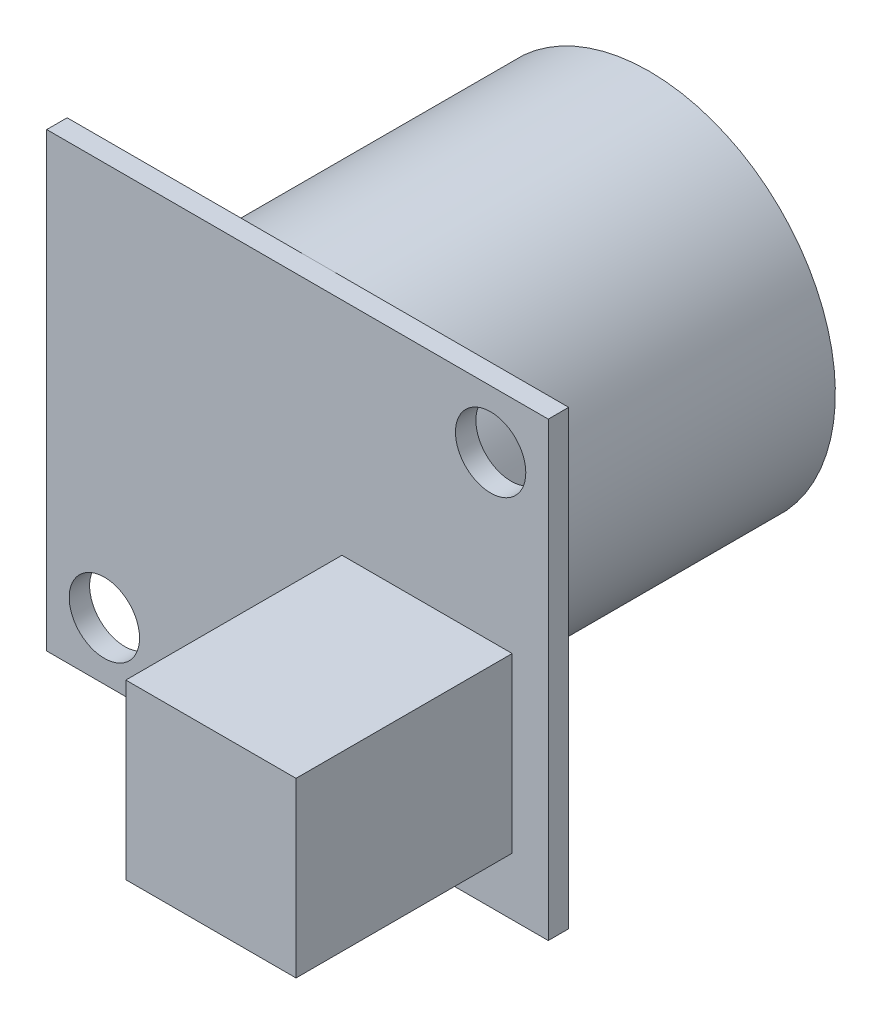
SolidWorks part; units mm, degrees
ref_plane "Front Plane" through (0, 0, 0) normal (0, 0, 1) x (1, 0, 0)
ref_plane "Top Plane" through (0, 0, 0) normal (0, 1, 0) x (1, 0, 0)
ref_plane "Right Plane" through (0, 0, 0) normal (1, 0, 0) x (0, 0, -1)
sketch "Sketch2" plane through (0, 0, 0) normal (0, 0, 1) x (1, 0, 0)
  line L1 (-11.05, -9.95) -> (11.05, -9.95)
  line L2 (-11.05, -9.95) -> (-11.05, 9.95)
  line L3 (-11.05, 9.95) -> (11.05, 9.95)
  line L4 (11.05, -9.95) -> (11.05, 9.95)
  line L5 (-11.05, -9.95) -> (11.05, 9.95) construction
  line L6 (-11.05, 9.95) -> (11.05, -9.95) construction
  circle A0 centre (-8.51, -7.41) radius 1.55
  circle A1 centre (8.51, 7.41) radius 1.55
  point P0 (0, 0)
  dimension "D3" = 3.1
  dimension "D7" = 3.1
  dimension "D1" = 22.1
  dimension "D2" = 19.9
  dimension "D4" = 2.54
  dimension "D5" = 2.54
  dimension "D6" = 2.54
  dimension "D8" = 2.54
extrude "Boss-Extrude1" add sketch "Sketch2" along normal blind 0.9 contours A1 | A0 | L2 L3 L4 L1
sketch "Sketch3" plane through (0, 0, 0.9) normal (0, 0, 1) x (1, 0, 0)
  line L0 (-11.05, -9.95) -> (11.05, -9.95) construction
  line L1 (1.9602, 0.21) -> (9.4602, 0.21)
  line L2 (1.9602, 0.21) -> (1.9602, -7.41)
  line L3 (1.9602, -7.41) -> (9.4602, -7.41)
  line L4 (9.4602, 0.21) -> (9.4602, -7.41)
  dimension "D1" = 7.5
  dimension "D2" = 7.62
  dimension "D3" = 2.54
extrude "Boss-Extrude2" add sketch "Sketch3" along normal blind 9.525
sketch "Sketch4" plane through (0, 0, 0) normal (0, 0, -1) x (-1, 0, 0)
  line L0 (11.05, 9.95) -> (-11.05, 9.95) construction
  line L2 (-11.05, 1.75) -> (11.05, 1.75) construction
  line L3 (-11.05, -9.95) -> (-11.05, 9.95) construction
  line L4 (11.05, -9.95) -> (11.05, 9.95) construction
  circle A0 centre (0, 1.75) radius 8.2
  point P12 (0, 1.75)
  dimension "D1" = 16.4
extrude "Boss-Extrude3" add sketch "Sketch4" along normal blind 14.6 contours A0
